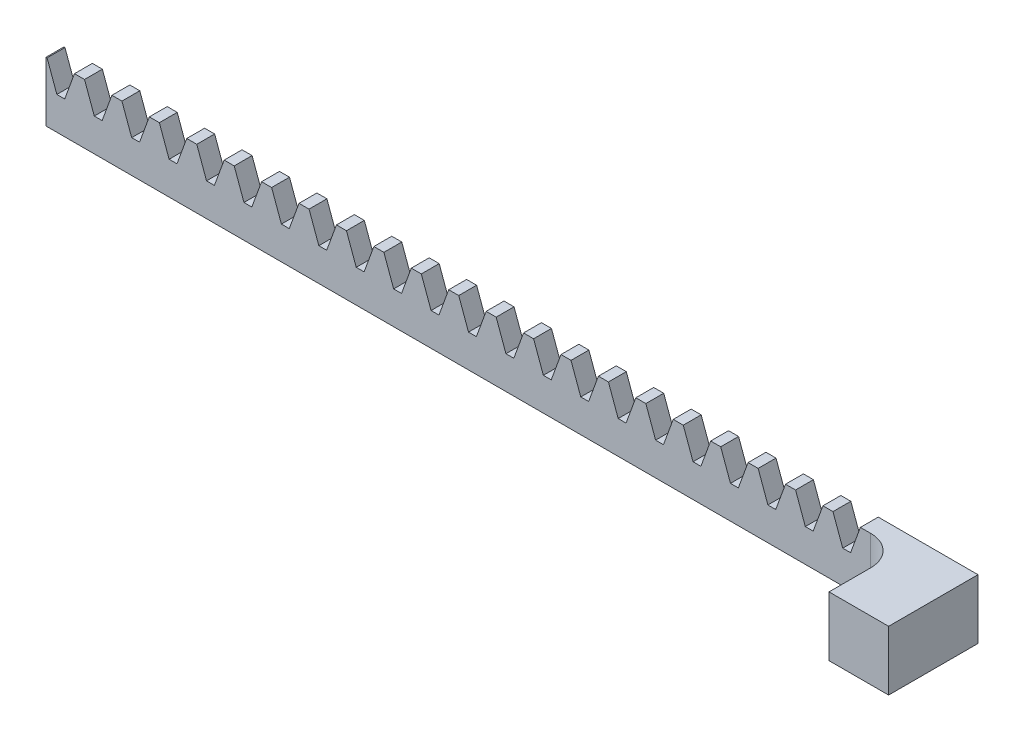
SolidWorks part; units mm, degrees
ref_plane "정면" through (0, 0, 0) normal (0, 0, 1) x (1, 0, 0)
ref_plane "윗면" through (0, 0, 0) normal (0, 1, 0) x (1, 0, 0)
ref_plane "우측면" through (0, 0, 0) normal (1, 0, 0) x (0, 0, -1)
sketch "스케치1" plane through (0, 0, 0) normal (0, 0, 1) x (1, 0, 0)
  line L1 (-76.7, 10) -> (76.7, 10)
  line L2 (-76.7, 10) -> (-76.7, 0)
  line L3 (-76.7, 0) -> (76.7, 0)
  line L4 (76.7, 10) -> (76.7, 0)
  dimension "D1" = 153.4
  dimension "D2" = 10
extrude "보스-돌출1" add sketch "스케치1" against normal blind 3
sketch "스케치2" plane through (0, 0, 0) normal (0, 0, 1) x (1, 0, 0)
  line L0 (-67.94, 10) -> (-67.94, 5.5) construction
  line L1 (-68.6001, 5.5) -> (-67.2799, 5.5)
  line L2 (-67.2799, 5.5) -> (-65.6421, 10)
  line L3 (-65.6421, 10) -> (-70.2379, 10)
  line L4 (-68.6001, 5.5) -> (-70.2379, 10)
  line L5 (-69.51, 8) -> (-66.37, 8)
  line L6 (-76.7, 10) -> (-76.7, 0) construction
  line L7 (76.7, 10) -> (-76.7, 10) construction
  line M10 (76.7, 10) -> (-76.7, 10)
  dimension "D1" = 2
  dimension "D2" = 4.5
  dimension "D3" = 40
  dimension "D4" = 8.76
  dimension "D5" = 3.14
extrude "컷-돌출1" cut sketch "스케치2" against normal through all contours L0 L3 L4 L5 | L0 L5 L2 M10 | L5 L0 L1 L2 | L0 L5 L4 L1
pattern_linear "선형 패턴1" count 21 spacing 6.28 along (1, 0, 0) count 2 spacing 6.28 along (-1, 0, 0) of "컷-돌출1"
sketch "스케치3" plane through (0, 0, 0) normal (0, -1, 0) x (1, 0, 0)
  line L1 (76.7, -3) -> (66.7, -3)
  line L2 (76.7, -3) -> (76.7, 12)
  line L3 (76.7, 12) -> (66.7, 12)
  line L4 (66.7, -3) -> (66.7, 12)
  dimension "D1" = 10
  dimension "D2" = 15
extrude "보스-돌출2" add sketch "스케치3" against normal blind 10
fillet "필렛1" radius 5 1 edges at (66.7, 5, 0)
sketch "스케치4" plane through (0, 0, 0) normal (0, -1, 0) x (1, 0, 0)
  line L0 (76.7, 12) -> (66.7, 12) construction
  line L1 (76.7, -3) -> (76.7, 12) construction
  circle A0 centre (71.7, 9) radius 1.25
  dimension "D1" = 2.5
  dimension "D2" = 3
  dimension "D3" = 5
extrude "컷-돌출2" cut sketch "스케치4" against normal blind 5.5
